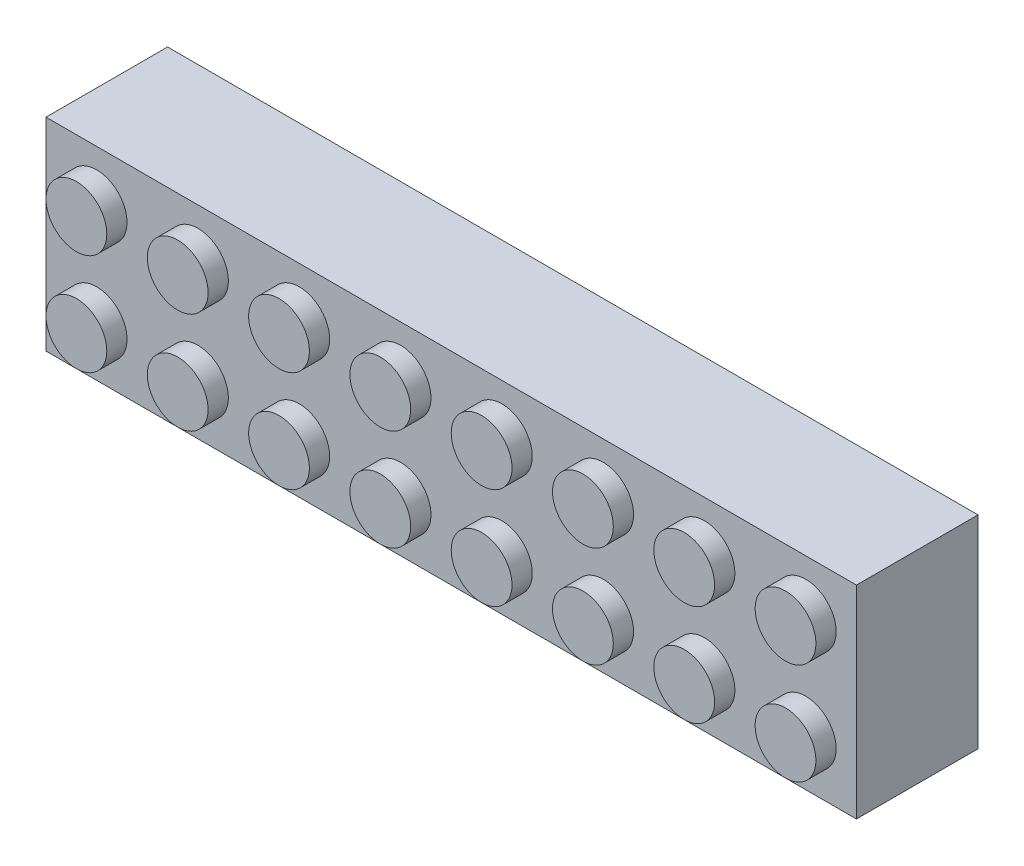
SolidWorks part; units mm, degrees
ref_plane "Front Plane" through (0, 0, 0) normal (0, 0, 1) x (1, 0, 0)
ref_plane "Top Plane" through (0, 0, 0) normal (0, 1, 0) x (1, 0, 0)
ref_plane "Right Plane" through (0, 0, 0) normal (1, 0, 0) x (0, 0, -1)
sketch "Sketch1" plane through (0, 0, 0) normal (0, 0, 1) x (1, 0, 0)
  line L1 (0, 0) -> (64, 0)
  line L2 (0, 0) -> (0, 16)
  line L3 (0, 16) -> (64, 16)
  line L4 (64, 0) -> (64, 16)
  dimension "D1" = 16
  dimension "D2" = 64
extrude "Boss-Extrude1" add sketch "Sketch1" along normal blind 9.6
sketch "Sketch2" plane through (0, 0, 9.6) normal (0, 0, 1) x (1, 0, 0)
  line L0 (64, 16) -> (0, 16) construction
  line L1 (0, 16) -> (0, 0) construction
  circle A0 centre (4, 12) radius 2.4
  dimension "D1" = 4.8
  dimension "D2" = 1.6
  dimension "D3" = 1.6
extrude "Boss-Extrude2" add sketch "Sketch2" along normal blind 1.6
pattern_linear "LPattern1" count 8 spacing 8 along (1, 0, 0) count 2 spacing 8 along (0, -1, 0) of "Boss-Extrude2"
shell "Shell1" thickness 1.6
sketch "Sketch3" plane through (0, 0, 8) normal (0, 0, -1) x (-1, 0, 0)
  line L0 (0, 0) -> (-64, 0) construction
  line L1 (0, 16) -> (0, 0) construction
  circle A0 centre (-8, 8) radius 3.256
  circle A1 centre (-8, 8) radius 2.4
  dimension "D1" = 4.8
  dimension "D2" = 6.512
  dimension "D3" = 8
  dimension "D4" = 8
extrude "Boss-Extrude3" add sketch "Sketch3" along normal blind 8
pattern_linear "LPattern2" count 7 spacing 8 along (1, 0, 0) of "Boss-Extrude3"
